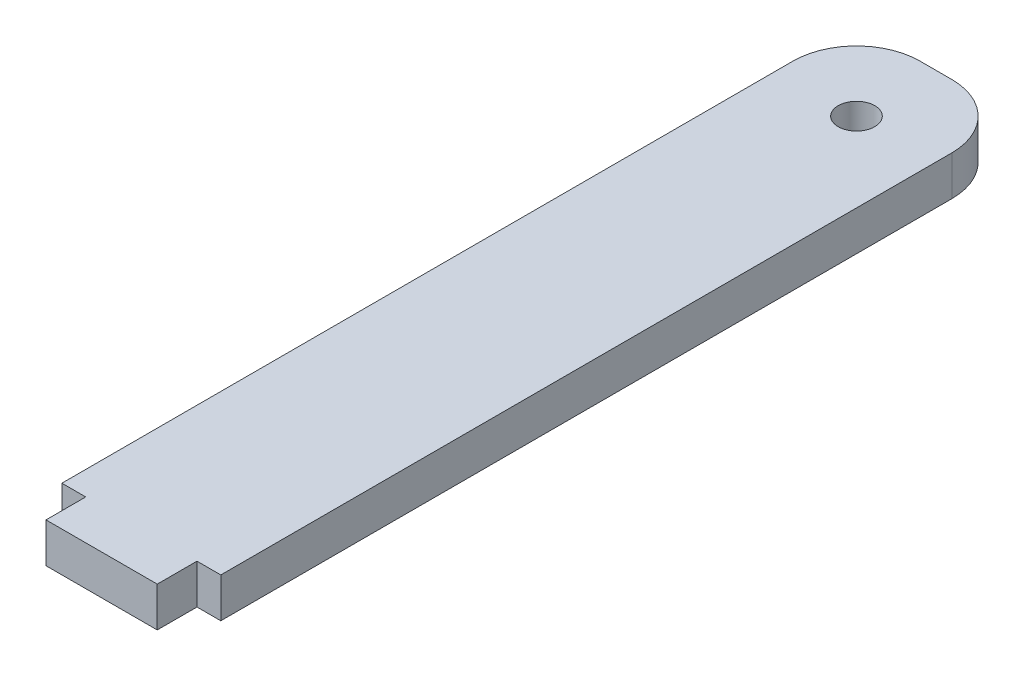
SolidWorks part; units mm, degrees
ref_plane "Front Plane" through (0, 0, 0) normal (0, 0, 1) x (1, 0, 0)
ref_plane "Top Plane" through (0, 0, 0) normal (0, 1, 0) x (1, 0, 0)
ref_plane "Right Plane" through (0, 0, 0) normal (1, 0, 0) x (0, 0, -1)
sketch "Sketch2" plane through (0, 0, 0) normal (0, 1, 0) x (1, 0, 0)
  line L0 (-4.445, -31.75) -> (-4.445, -34.925)
  line L1 (6.35, 31.75) -> (-6.35, 31.75)
  line L2 (6.35, 31.75) -> (6.35, -31.75)
  line L3 (6.35, -31.75) -> (-6.35, -31.75)
  line L4 (-6.35, 31.75) -> (-6.35, -31.75)
  line L5 (6.35, 31.75) -> (-6.35, -31.75) construction
  line L6 (6.35, -31.75) -> (-6.35, 31.75) construction
  line L7 (-4.445, -34.925) -> (4.445, -34.925)
  line L8 (4.445, -34.925) -> (4.445, -31.75)
  line L9 (0, 0) -> (0, 6.4453) construction
  circle A0 centre (0, 25.4) radius 1.4605
  point P0 (0, 0)
  dimension "D5" = 2.921
  dimension "D1" = 12.7
  dimension "D2" = 8.89
  dimension "D3" = 3.175
  dimension "D4" = 63.5
  dimension "D6" = 6.35
extrude "Boss-Extrude1" add sketch "Sketch2" along normal mid plane 3.175 contours L1 L4 L3 L2 | L7 L8 L3 L0
fillet "Fillet1" radius 5.08 2 edges at (6.35, 0, -31.75) (-6.35, 0, -31.75)
